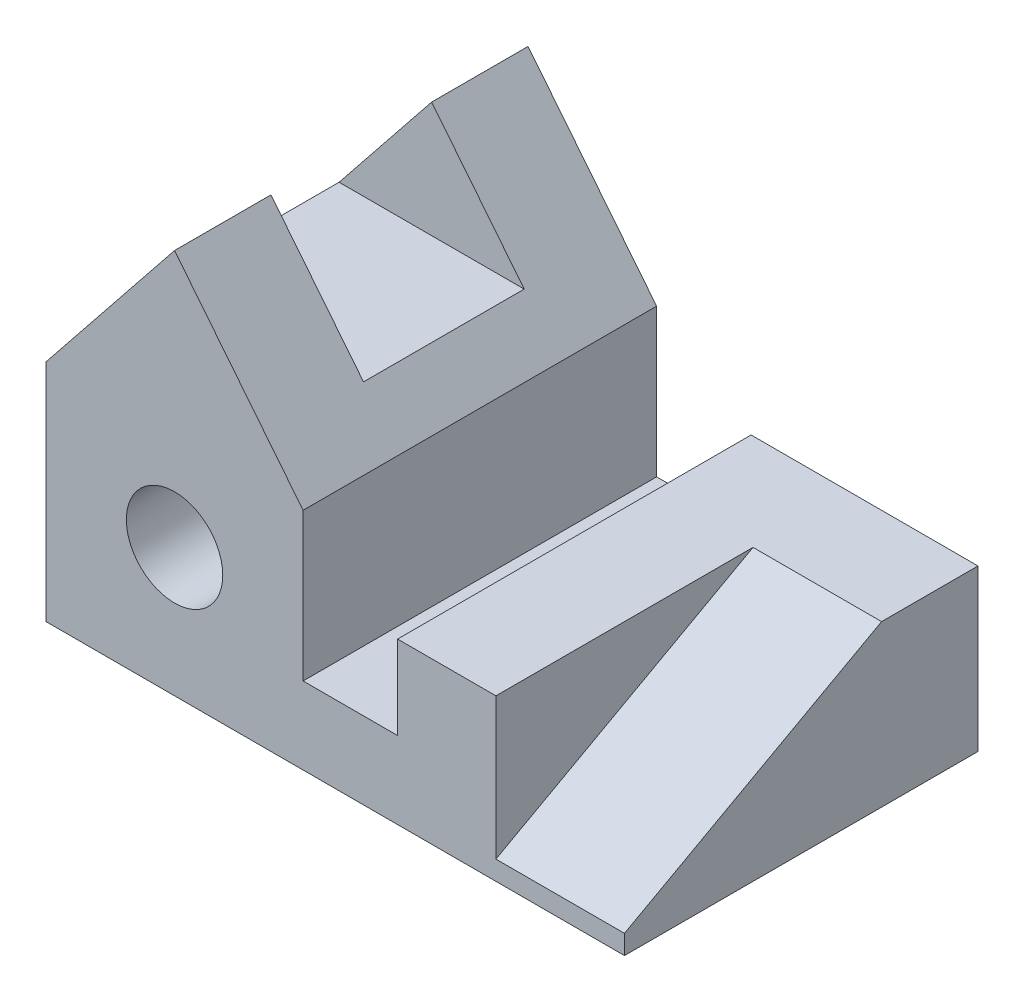
SolidWorks part; units mm, degrees
ref_plane "Front Plane" through (0, 0, 0) normal (0, 0, 1) x (1, 0, 0)
ref_plane "Top Plane" through (0, 0, 0) normal (0, 1, 0) x (1, 0, 0)
ref_plane "Right Plane" through (0, 0, 0) normal (1, 0, 0) x (0, 0, -1)
sketch "Sketch1" plane through (0, 0, 0) normal (0, 1, 0) x (1, 0, 0)
  line L0 (-1143, 698.5) -> (1143, 698.5)
  line L1 (1143, 698.5) -> (1143, -698.5)
  line L2 (1143, -698.5) -> (-1143, -698.5)
  line L3 (-1143, -698.5) -> (-1143, 698.5)
  dimension "D1" = 2286
  dimension "D2" = 1397
  dimension "D3" = 1143
  dimension "D4" = 698.5
extrude "Boss-Extrude1" add sketch "Sketch1" along normal blind 1524 contours L3 L0 L1 L2
sketch "Sketch2" plane through (0, 0, 698.5) normal (0, 0, 1) x (1, 0, 0)
  line L1 (-1143, 1524) -> (-1143, 0) construction
  line L2 (-1143, 889) -> (-635, 1524)
  line L3 (1143, 1524) -> (-1143, 1524) construction
  line L5 (-127, 889) -> (-127, 304.8)
  line L6 (-127, 889) -> (-635, 1524)
  line L10 (-127, 304.8) -> (246.4055, 304.8)
  line L11 (246.4055, 304.8) -> (246.4055, 635)
  line L12 (246.4055, 635) -> (1143, 635)
  line L14 (1143, 1524) -> (1143, 0) construction
  line L15 (1143, 0) -> (-1143, 0) construction
  dimension "D2" = 304.8
  dimension "D4" = 508
  dimension "D5" = 635
extrude "Cut-Extrude7" cut sketch "Sketch2" against normal blind 1397 and the other way through all contours L2 L6 L5 L10 L11 L12
sketch "Sketch3" plane through (0, 0, 698.5) normal (0, 0, 1) x (1, 0, 0)
  circle A0 centre (-635, 508) radius 190.5
  dimension "D1" = 381
  dimension "D2" = 508
  dimension "D3" = 508
extrude "Cut-Extrude8" cut sketch "Sketch3" against normal through all
sketch "Sketch8" plane through (0, 0, 0) normal (0, 0, 1) x (1, 0, 0)
  line L1 (-635, 1066.8) -> (-1000.76, 1066.8)
  line L2 (-1143, 889) -> (-635, 1524) construction
  line L3 (-1000.76, 1066.8) -> (-635, 1524)
  line L4 (-635, 1066.8) -> (-269.24, 1066.8)
  line L5 (-635, 1524) -> (-127, 889) construction
  line L6 (-269.24, 1066.8) -> (-635, 1524)
  dimension "D1" = 457.2
extrude "Cut-Extrude9" cut sketch "Sketch8" against normal blind 317.5 and the other way blind 317.5
sketch "Sketch9" plane through (1143, 0, 0) normal (1, 0, 0) x (0, 0, -1)
  line L6 (-698.5, 635) -> (698.5, 635) construction
  line L7 (317.5, 635) -> (-698.5, 76.2)
  line L8 (-698.5, 635) -> (-698.5, 0) construction
  line L9 (317.5, 635) -> (-698.5, 635)
  line L10 (-698.5, 635) -> (-698.5, 76.2)
  dimension "D2" = 558.8
extrude "Cut-Extrude10" cut sketch "Sketch9" against normal blind 508
